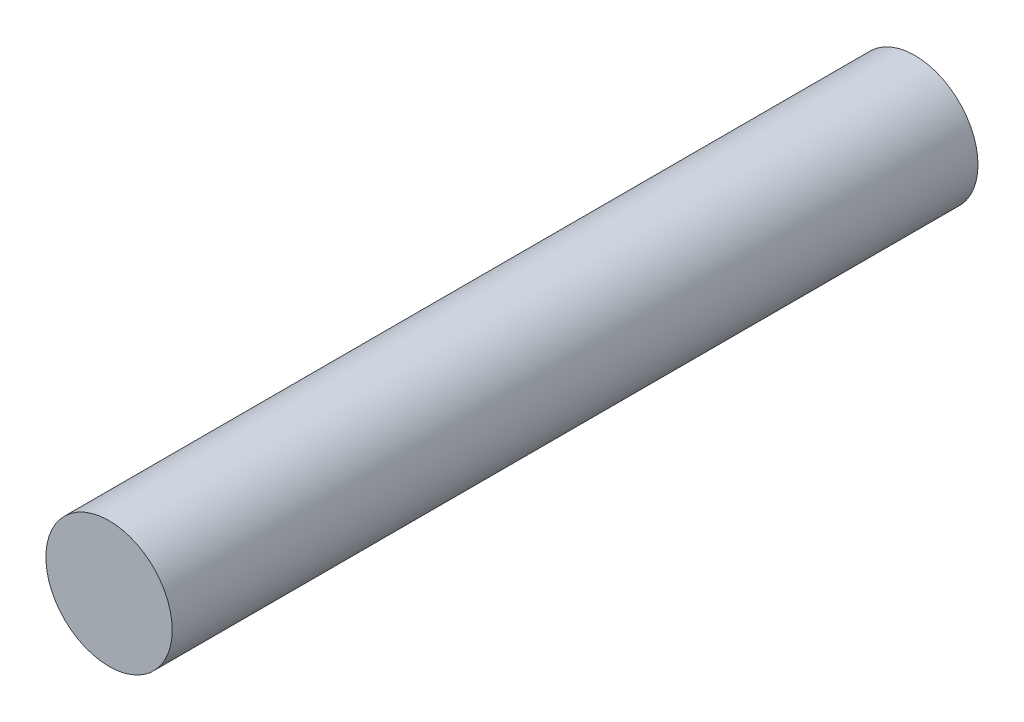
SolidWorks part; units mm, degrees
ref_plane "Front Plane" through (0, 0, 0) normal (0, 0, 1) x (1, 0, 0)
ref_plane "Top Plane" through (0, 0, 0) normal (0, 1, 0) x (1, 0, 0)
ref_plane "Right Plane" through (0, 0, 0) normal (1, 0, 0) x (0, 0, -1)
surface "Surface-Offset1" parameters "D1"=0
ref_plane "Plane1" through (0, 0, 58.1635) normal (0, 0, 1) x (1, 0, 0)
ref_plane "Plane2" through (0, 0, -22.86) normal (0, 0, 1) x (1, 0, 0)
sketch "Sketch3" plane through (0, 0, 58.1635) normal (0, 0, 1) x (1, 0, 0)
  circle A0 centre (-36.068, 0) radius 6.35 construction
  circle A1 centre (-36.068, 0) radius 6.35
extrude "Boss-Extrude1" add sketch "Sketch3" against normal up to surface (81.0235 mm away) up to plane "Plane2"
